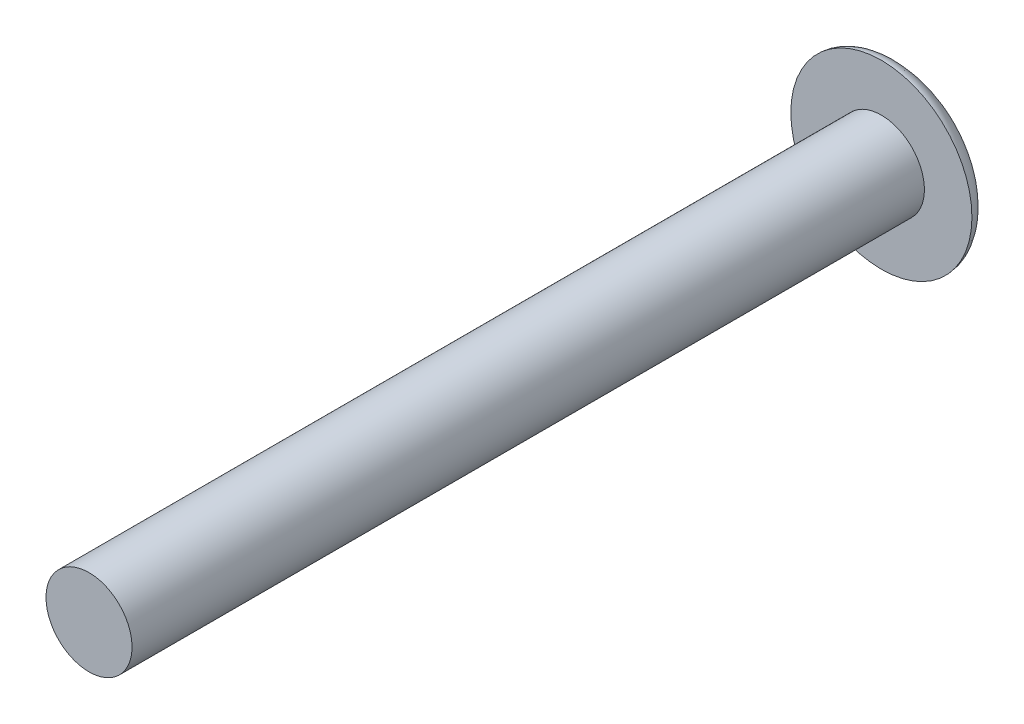
SolidWorks part; units mm, degrees
ref_plane "Plano frontal" through (0, 0, 0) normal (0, 0, 1) x (1, 0, 0)
ref_plane "Plano superior" through (0, 0, 0) normal (0, 1, 0) x (1, 0, 0)
ref_plane "Plano direito" through (0, 0, 0) normal (1, 0, 0) x (0, 0, -1)
sketch "Esboço1" plane through (0, 0, 0) normal (0, 1, 0) x (1, 0, 0)
  line L0 (1.9, 0) -> (4, 0)
  line L1 (0, 0) -> (0, -35)
  line L2 (0, -35) -> (1.9, -35)
  line L3 (1.9, -35) -> (1.9, 0)
  line L4 (0, 0) -> (0, 1.5)
  ellipse E0 centre (0, 0) end of major axis (4, 0) minor radius 1.5 (4, 0) -> (0, 1.5) ccw
revolve "Revolução1" add sketch "Esboço1" angle 360 about L1
sketch "Esboço2" plane through (0, 0, 0) normal (0, 0, 1) x (1, 0, 0)
  line L1 (4.6, 0.5) -> (-4.6, 0.5)
  line L2 (4.6, 0.5) -> (4.6, -0.5)
  line L3 (4.6, -0.5) -> (-4.6, -0.5)
  line L4 (-4.6, 0.5) -> (-4.6, -0.5)
  line L5 (4.6, 0.5) -> (-4.6, -0.5) construction
  line L6 (4.6, -0.5) -> (-4.6, 0.5) construction
  point P0 (0, 0)
extrude "Corte-extrusão1" cut sketch "Esboço2" against normal blind 10 from offset 0.5
